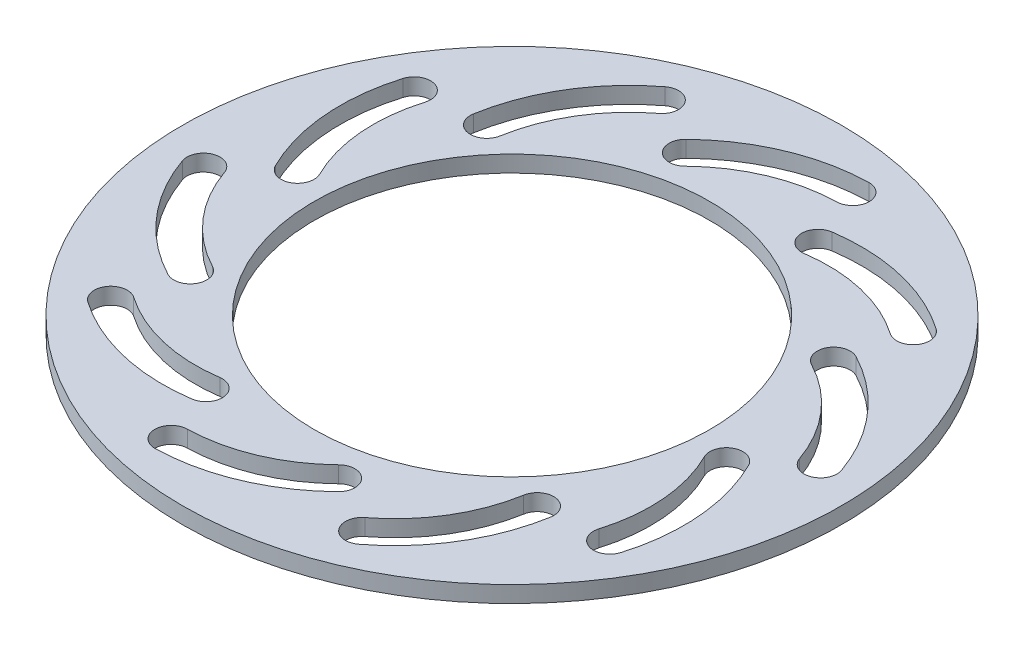
SolidWorks part; units mm, degrees
ref_plane "Front Plane" through (0, 0, 0) normal (0, 0, 1) x (1, 0, 0)
ref_plane "Top Plane" through (0, 0, 0) normal (0, 1, 0) x (1, 0, 0)
ref_plane "Right Plane" through (0, 0, 0) normal (1, 0, 0) x (0, 0, -1)
sketch "Sketch2" plane through (0, 0, 0) normal (0, 1, 0) x (1, 0, 0)
  line L0 (0, 0) -> (0, 100) construction
  circle A0 centre (0, 0) radius 100
  circle A1 centre (0, 0) radius 60
  circle A2 centre (0, 0) radius 80 construction
  arc A3 (-16.4237, 69.108) -> (19.2743, 84.108) centre (20.4455, 31.3424) cw construction
  arc A4 (19.1633, 89.1068) -> (-19.9165, 72.6857) centre (20.4455, 31.3424) ccw
  arc A5 (19.3852, 79.1092) -> (-12.9309, 65.5303) centre (20.4455, 31.3424) ccw
  arc A6 (19.3852, 79.1092) -> (19.1633, 89.1068) centre (19.2743, 84.108) ccw
  arc A7 (-19.9165, 72.6857) -> (-12.9309, 65.5303) centre (-16.4237, 69.108) ccw
  arc A8 (27.3336, 65.5632) -> (65.0307, 56.7157) centre (34.9634, 13.339) cw construction
  arc A9 (67.8791, 60.825) -> (26.6108, 70.5106) centre (34.9634, 13.339) ccw
  arc A10 (62.1822, 52.6064) -> (28.0564, 60.6157) centre (34.9634, 13.339) ccw
  arc A11 (62.1822, 52.6064) -> (67.8791, 60.825) centre (65.0307, 56.7157) ccw
  arc A12 (26.6108, 70.5106) -> (28.0564, 60.6157) centre (27.3336, 65.5632) ccw
  arc A13 (60.6504, 36.9754) -> (85.9475, 7.6599) centre (36.1264, -9.7595) cw construction
  arc A14 (90.6674, 9.3101) -> (62.9737, 41.4029) centre (36.1264, -9.7595) ccw
  arc A15 (81.2277, 6.0096) -> (58.3271, 32.548) centre (36.1264, -9.7595) ccw
  arc A16 (81.2277, 6.0096) -> (90.6674, 9.3101) centre (85.9475, 7.6599) ccw
  arc A17 (62.9737, 41.4029) -> (58.3271, 32.548) centre (60.6504, 36.9754) ccw
  arc A18 (70.8008, -5.7357) -> (74.0354, -44.3217) centre (23.4904, -29.1302) cw construction
  arc A19 (78.8238, -45.7609) -> (75.2828, -3.5194) centre (23.4904, -29.1302) ccw
  arc A20 (69.247, -42.8826) -> (66.3189, -7.952) centre (23.4904, -29.1302) ccw
  arc A21 (69.247, -42.8826) -> (78.8238, -45.7609) centre (74.0354, -44.3217) ccw
  arc A22 (75.2828, -3.5194) -> (66.3189, -7.952) centre (70.8008, -5.7357) ccw
  arc A23 (53.9077, -46.2559) -> (33.8442, -79.3739) centre (1.8819, -37.3741) cw construction
  arc A24 (36.8722, -83.3528) -> (58.8364, -47.0974) centre (1.8819, -37.3741) ccw
  arc A25 (30.8163, -75.3951) -> (48.979, -45.4145) centre (1.8819, -37.3741) ccw
  arc A26 (30.8163, -75.3951) -> (36.8722, -83.3528) centre (33.8442, -79.3739) ccw
  arc A27 (58.8364, -47.0974) -> (48.979, -45.4145) centre (53.9077, -46.2559) ccw
  arc A28 (16.4237, -69.108) -> (-19.2743, -84.108) centre (-20.4455, -31.3424) cw construction
  arc A29 (-19.1633, -89.1068) -> (19.9165, -72.6857) centre (-20.4455, -31.3424) ccw
  arc A30 (-19.3852, -79.1092) -> (12.9309, -65.5303) centre (-20.4455, -31.3424) ccw
  arc A31 (-19.3852, -79.1092) -> (-19.1633, -89.1068) centre (-19.2743, -84.108) ccw
  arc A32 (19.9165, -72.6857) -> (12.9309, -65.5303) centre (16.4237, -69.108) ccw
  arc A33 (-27.3336, -65.5632) -> (-65.0307, -56.7157) centre (-34.9634, -13.339) cw construction
  arc A34 (-67.8791, -60.825) -> (-26.6108, -70.5106) centre (-34.9634, -13.339) ccw
  arc A35 (-62.1822, -52.6064) -> (-28.0564, -60.6157) centre (-34.9634, -13.339) ccw
  arc A36 (-62.1822, -52.6064) -> (-67.8791, -60.825) centre (-65.0307, -56.7157) ccw
  arc A37 (-26.6108, -70.5106) -> (-28.0564, -60.6157) centre (-27.3336, -65.5632) ccw
  arc A38 (-60.6504, -36.9754) -> (-85.9475, -7.6599) centre (-36.1264, 9.7595) cw construction
  arc A39 (-90.6674, -9.3101) -> (-62.9737, -41.4029) centre (-36.1264, 9.7595) ccw
  arc A40 (-81.2277, -6.0096) -> (-58.3271, -32.548) centre (-36.1264, 9.7595) ccw
  arc A41 (-81.2277, -6.0096) -> (-90.6674, -9.3101) centre (-85.9475, -7.6599) ccw
  arc A42 (-62.9737, -41.4029) -> (-58.3271, -32.548) centre (-60.6504, -36.9754) ccw
  arc A43 (-70.8008, 5.7357) -> (-74.0354, 44.3217) centre (-23.4904, 29.1302) cw construction
  arc A44 (-78.8238, 45.7609) -> (-75.2828, 3.5194) centre (-23.4904, 29.1302) ccw
  arc A45 (-69.247, 42.8826) -> (-66.3189, 7.952) centre (-23.4904, 29.1302) ccw
  arc A46 (-69.247, 42.8826) -> (-78.8238, 45.7609) centre (-74.0354, 44.3217) ccw
  arc A47 (-75.2828, 3.5194) -> (-66.3189, 7.952) centre (-70.8008, 5.7357) ccw
  arc A48 (-53.9077, 46.2559) -> (-33.8442, 79.3739) centre (-1.8819, 37.3741) cw construction
  arc A49 (-36.8722, 83.3528) -> (-58.8364, 47.0974) centre (-1.8819, 37.3741) ccw
  arc A50 (-30.8163, 75.3951) -> (-48.979, 45.4145) centre (-1.8819, 37.3741) ccw
  arc A51 (-30.8163, 75.3951) -> (-36.8722, 83.3528) centre (-33.8442, 79.3739) ccw
  arc A52 (-58.8364, 47.0974) -> (-48.979, 45.4145) centre (-53.9077, 46.2559) ccw
  point P9 (0, 80)
  point P20 (47.0228, 64.7214)
  point P28 (76.0845, 24.7214)
  point P36 (76.0845, -24.7214)
  point P44 (47.0228, -64.7214)
  point P52 (0, -80)
  point P60 (-47.0228, -64.7214)
  point P68 (-76.0845, -24.7214)
  point P76 (-76.0845, 24.7214)
  point P84 (-47.0228, 64.7214)
  point P89 (0, 0)
  dimension "D1" = 200
  dimension "D2" = 120
  dimension "D3" = 160
  dimension "D4" = 5
  dimension "D5" = 35.698
  dimension "D6" = 15
  dimension "D7" = 10
extrude "Boss-Extrude1" add sketch "Sketch2" along normal blind 5
